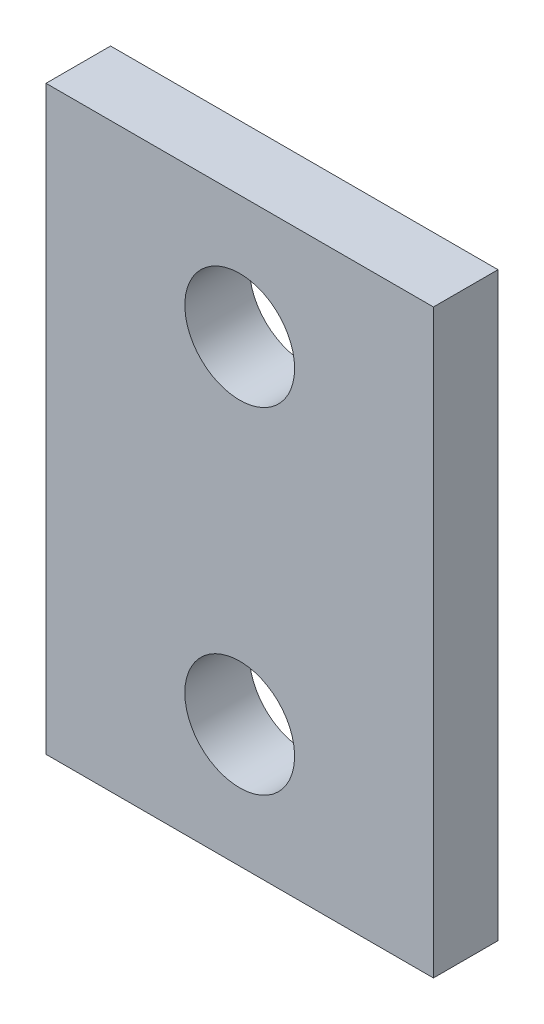
SolidWorks part; units mm, degrees
ref_plane "Front Plane" through (0, 0, 0) normal (0, 0, 1) x (1, 0, 0)
ref_plane "Top Plane" through (0, 0, 0) normal (0, 1, 0) x (1, 0, 0)
ref_plane "Right Plane" through (0, 0, 0) normal (1, 0, 0) x (0, 0, -1)
sketch "Sketch1" plane through (0, 0, 0) normal (0, 0, 1) x (1, 0, 0)
  line L0 (-23750, 0) -> (35454.5455, 0) construction
  line L1 (15, 22.5) -> (-15, 22.5)
  line L2 (15, 22.5) -> (15, -22.5)
  line L3 (15, -22.5) -> (-15, -22.5)
  line L4 (-15, 22.5) -> (-15, -22.5)
  line L5 (15, 22.5) -> (-15, -22.5) construction
  line L6 (15, -22.5) -> (-15, 22.5) construction
  line L7 (0, 13) -> (0, -13.2515) construction
  circle A0 centre (0, 13) radius 4.25
  circle A1 centre (0, -13) radius 4.25
  point P0 (0, 0)
  dimension "D3" = 8.5
  dimension "D1" = 30
  dimension "D2" = 45
  dimension "D4" = 13
extrude "Boss-Extrude1" add sketch "Sketch1" along normal blind 5
